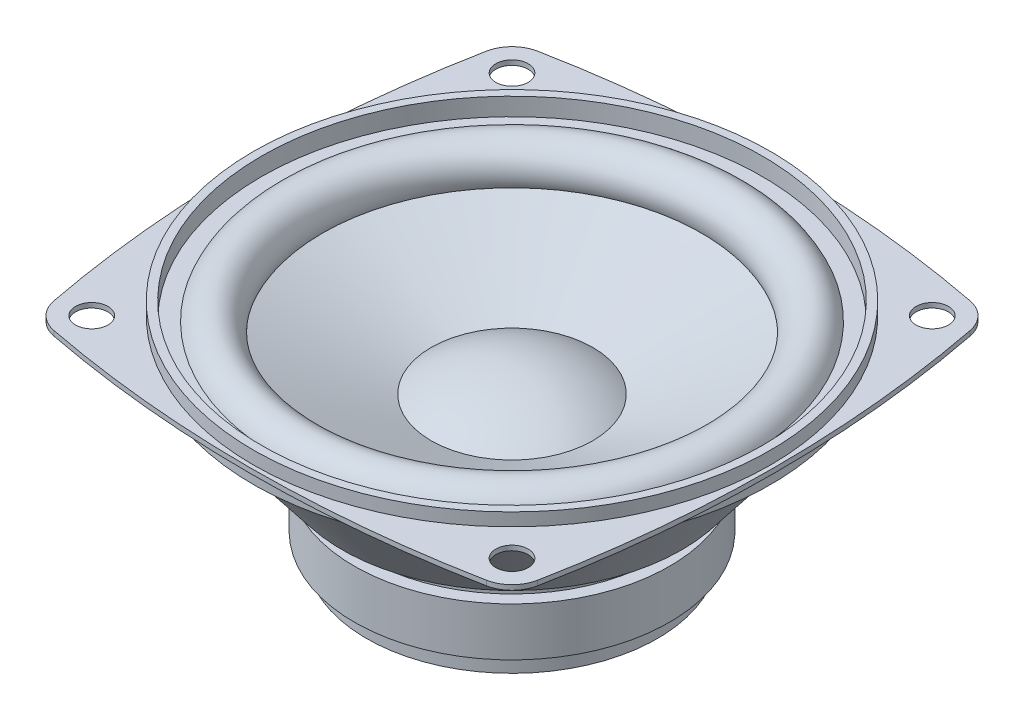
SolidWorks part; units mm, degrees
ref_plane "Front Plane" through (0, 0, 0) normal (0, 0, 1) x (1, 0, 0)
ref_plane "Top Plane" through (0, 0, 0) normal (0, 1, 0) x (1, 0, 0)
ref_plane "Right Plane" through (0, 0, 0) normal (1, 0, 0) x (0, 0, -1)
sketch "Sketch1" plane through (0, 0, 0) normal (0, 1, 0) x (1, 0, 0)
  line L1 (-26, 26) -> (26, 26) construction
  line L2 (-26, 26) -> (-26, -26) construction
  line L3 (-26, -26) -> (26, -26) construction
  line L4 (26, 26) -> (26, -26) construction
  circle A0 centre (0, 0) radius 32
  circle A1 centre (0, 0) radius 32.5 construction
  circle A2 centre (-26, 26) radius 2
  circle A3 centre (26, 26) radius 2
  circle A4 centre (26, -26) radius 2
  circle A5 centre (-26, -26) radius 2
  arc A6 (-26.7622, 29.9267) -> (-29.9267, 26.7622) centre (-26, 26) ccw
  arc A7 (29.9267, 26.7622) -> (26.7622, 29.9267) centre (26, 26) ccw
  arc A8 (26.7622, -29.9267) -> (29.9267, -26.7622) centre (26, -26) ccw
  arc A9 (-29.9267, -26.7622) -> (-26.7622, -29.9267) centre (-26, -26) ccw
  arc A10 (-26.7622, 29.9267) -> (26.7622, 29.9267) centre (0, -107.95) cw
  arc A11 (-29.9267, 26.7622) -> (-29.9267, -26.7622) centre (107.95, 0) ccw
  arc A12 (-26.7622, -29.9267) -> (26.7622, -29.9267) centre (0, 107.95) ccw
  arc A13 (29.9267, 26.7622) -> (29.9267, -26.7622) centre (-107.95, 0) cw
  point P8 (0, 26)
  point P9 (26, 0)
  dimension "D1" = 64
  dimension "D2" = 65
  dimension "D3" = 4
  dimension "D5" = 2
  dimension "D4" = 52
extrude "Boss-Extrude1" add sketch "Sketch1" along normal blind 0.6
sketch "Sketch2" plane through (0, 0, 0) normal (0, 0, 1) x (1, 0, 0)
  line L0 (32, -1.5) -> (32, 2.2)
  line L1 (32, 2.2) -> (31, 2.2)
  line L2 (31, 2.2) -> (31, 0)
  line L3 (31, 0) -> (29, 0)
  line L4 (32.5, 0.6) -> (29.9267, 0.6) construction
  line L5 (10, -7.8) -> (23.4495, -2.2786)
  line L6 (32, 0) -> (32, 0.6) construction
  line L7 (32, -1.5) -> (30, -1.5)
  line L8 (30, -1.5) -> (30, -2.5)
  line L9 (30, -2.5) -> (21, -14)
  line L10 (21, -14) -> (18, -14)
  line L11 (18, -14) -> (18, -16.5)
  line L12 (18, -16.5) -> (19.5, -16.5)
  line L13 (19.5, -16.5) -> (19.5, -22.5)
  line L14 (19.5, -22.5) -> (18, -22.5)
  line L15 (18, -22.5) -> (18, -25)
  line L16 (18, -25) -> (0, -25)
  line L17 (0, -25) -> (0, -4.8)
  line L18 (0, -17.4796) -> (0, -25.8251) construction
  line L19 (-32, 0) -> (32, 0) construction
  arc A0 (29, 0) -> (23.4495, -2.2786) centre (26.2248, -1.1393) ccw
  arc A1 (0, -4.8) -> (10, -7.8) centre (0, -22.9667) cw
  dimension "D1" = 1.6
  dimension "D2" = 1
  dimension "D3" = 2
  dimension "D4" = 6
  dimension "D5" = 10
  dimension "D6" = 3
  dimension "D7" = 10
  dimension "D8" = 1.5
  dimension "D9" = 36
  dimension "D10" = 39
  dimension "D11" = 2.5
  dimension "D12" = 25
  dimension "D13" = 6
  dimension "D14" = 42
  dimension "D15" = 2
  dimension "D16" = 1
revolve "Revolve1" add sketch "Sketch2" angle 360 about L18
sketch "Sketch3" plane through (0, 0, 0) normal (1, 0, 0) x (0, 0, -1)
  line L0 (29.7385, -6.0793) -> (28.1635, -4.8467)
  line L1 (29.7385, -6.0793) -> (24.808, -12.3793)
  line L2 (28.1635, -4.8467) -> (23.233, -11.1467)
  line L3 (24.808, -12.3793) -> (23.233, -11.1467)
  line L4 (21, -14) -> (30, -2.5) construction
  dimension "D1" = 8
  dimension "D2" = 2
  dimension "D3" = 5
extrude "Boss-Extrude2" add sketch "Sketch3" along normal mid plane 25 separate body
sketch "Sketch4" plane through (12.5, 0, 0) normal (1, 0, 0) x (0, 0, -1)
  line L0 (24.808, -12.3793) -> (29.7385, -6.0793) construction
  circle A0 centre (27.2733, -9.2293) radius 1.0566
extrude "Boss-Extrude3" add sketch "Sketch4" along normal blind 8 and the other way blind 4
mirror "Mirror1" about plane through (0, 0, 0) normal (1, 0, 0) of "Boss-Extrude3"
